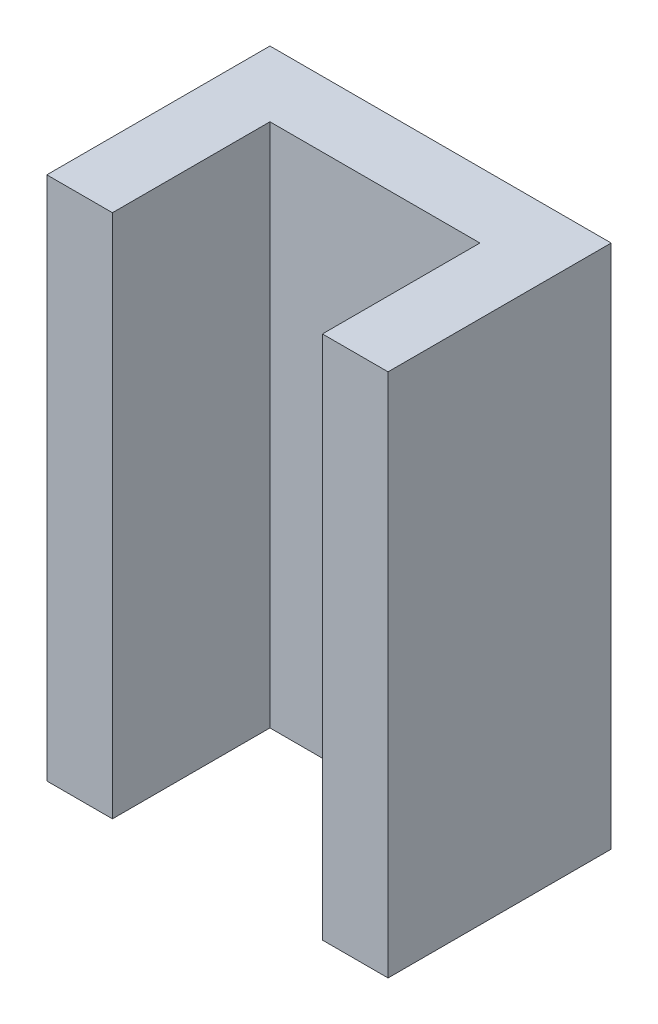
SolidWorks part; units mm, degrees
ref_plane "Front Plane" through (0, 0, 0) normal (0, 0, 1) x (1, 0, 0)
ref_plane "Top Plane" through (0, 0, 0) normal (0, 1, 0) x (1, 0, 0)
ref_plane "Right Plane" through (0, 0, 0) normal (1, 0, 0) x (0, 0, -1)
sketch "Sketch1" plane through (0, 0, 0) normal (0, 1, 0) x (1, 0, 0)
  line L0 (0, 0) -> (0, 8.5)
  line L1 (13, 8.5) -> (0, 8.5)
  line L2 (13, 8.5) -> (13, 0)
  line L3 (0, 0) -> (2.5, 0)
  line L4 (2.5, 0) -> (2.5, 6)
  line L5 (2.5, 6) -> (10.5, 6)
  line L6 (10.5, 6) -> (10.5, 0)
  line L7 (10.5, 0) -> (13, 0)
  dimension "D1" = 2.5
  dimension "D2" = 2.5
  dimension "D3" = 2.5
  dimension "D4" = 8
  dimension "D5" = 6
  dimension "D6" = 6
extrude "Boss-Extrude1" add sketch "Sketch1" along normal blind 20
